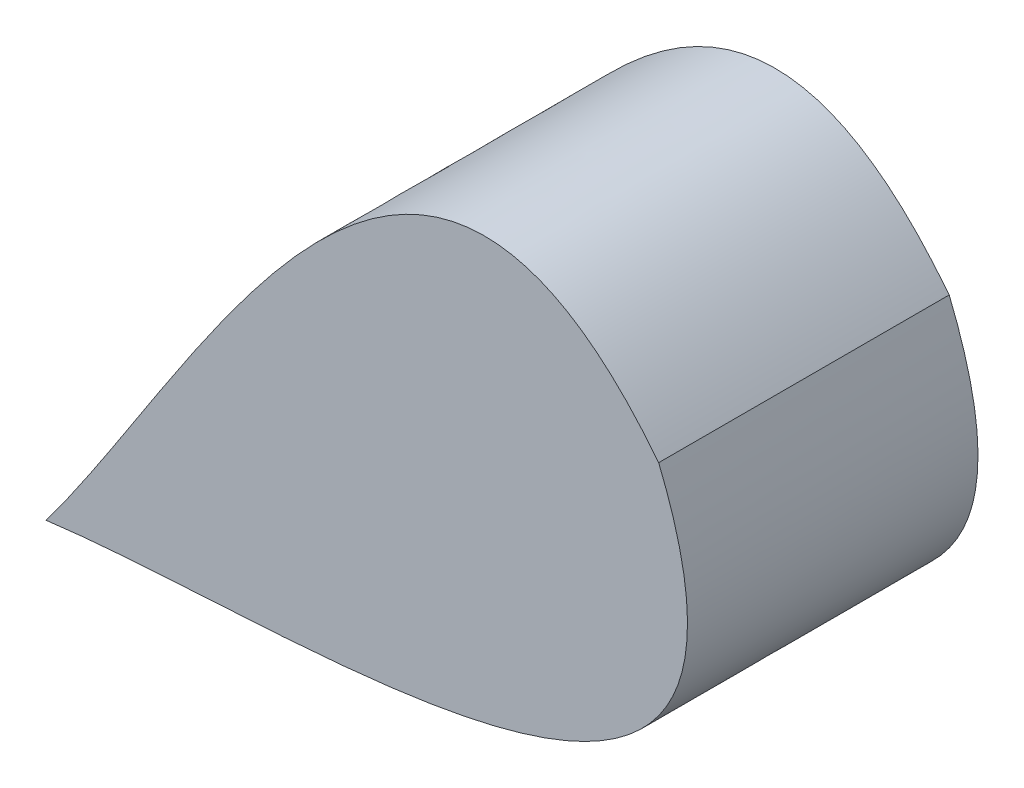
SolidWorks part; units mm, degrees
ref_plane "Front Plane" through (0, 0, 0) normal (0, 0, 1) x (1, 0, 0)
ref_plane "Top Plane" through (0, 0, 0) normal (0, 1, 0) x (1, 0, 0)
ref_plane "Right Plane" through (0, 0, 0) normal (1, 0, 0) x (0, 0, -1)
sketch "Sketch1" plane through (0, 0, 0) normal (0, 0, 1) x (1, 0, 0)
  line L0 (318.6667, 759.5) -> (1593.3333, 759.5) construction
  line L1 (213.3046, 332.0385) -> (1663.6294, 1175.199) construction
  spline S0 degree 3 poles (948.0901, 759.2132) (953.5317, 766.4019) (960.5402, 782.5304) (969.1799, 771.474) knots 0 0 0 0 1 1 1 1
  spline S1 degree 3 poles (948.0901, 759.2132) (957.0296, 760.3851) (974.5132, 758.4954) (969.1799, 771.474) knots 0 0 0 0 1 1 1 1
extrude "Boss-Extrude1" add sketch "Sketch1" along normal blind 10
